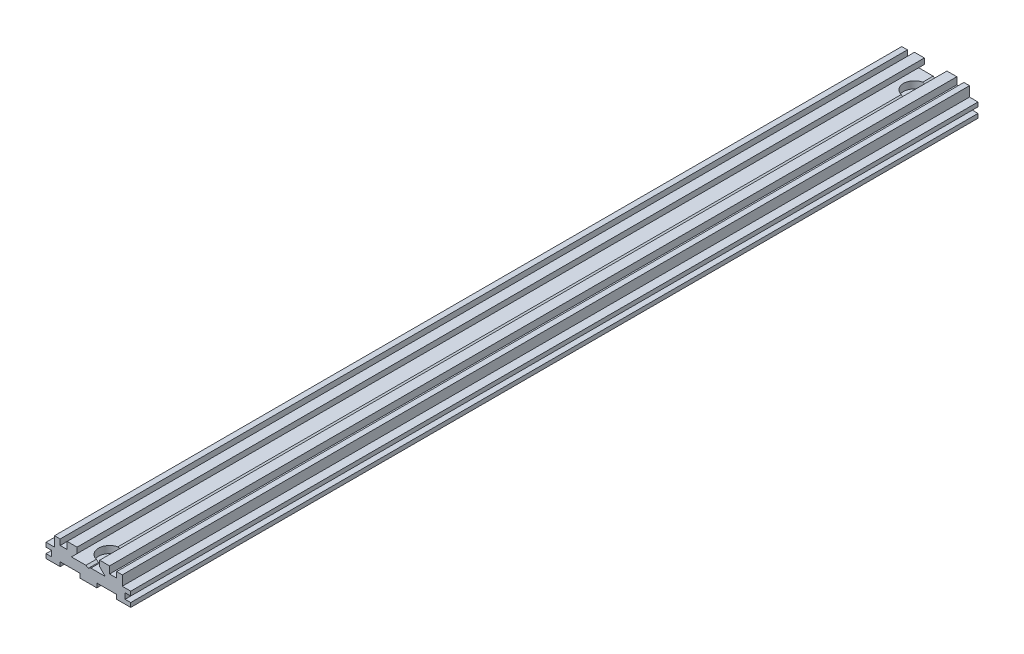
SolidWorks part; units mm, degrees
material "6061 合金"
ref_plane "前视基准面" through (0, 0, 0) normal (0, 0, 1) x (1, 0, 0)
ref_plane "上视基准面" through (0, 0, 0) normal (0, 1, 0) x (1, 0, 0)
ref_plane "右视基准面" through (0, 0, 0) normal (1, 0, 0) x (0, 0, -1)
sketch "草图1" plane through (0, 0, 0) normal (0, 0, 1) x (1, 0, 0)
  line L0 (7.5, 9) -> (7.5, 6.5)
  line L1 (7.5, 6.5) -> (5, 6.5)
  line L2 (5, 6.5) -> (5, 8.5)
  line L3 (30, 0) -> (0, 0)
  line L4 (0, 0) -> (0, 1.5)
  line L5 (15, 0) -> (15, 16.1171) construction
  line L6 (11, 7) -> (9, 5)
  line L7 (19, 7) -> (21, 5)
  line L8 (21, 5) -> (9, 5)
  line L9 (0, 3.5) -> (0, 5)
  line L10 (0, 3.5) -> (2, 3.5)
  line L11 (11, 7) -> (11, 9)
  line L12 (11, 9) -> (7.5, 9)
  line L13 (5, 8.5) -> (3, 8.5)
  line L14 (30, 5) -> (27, 5)
  line L15 (3, 5) -> (0, 5)
  line L16 (19, 7) -> (19, 9)
  line L17 (3, 8.5) -> (3, 5)
  line L18 (22.5, 9) -> (19, 9)
  line L19 (30, 5) -> (0, 5) construction
  line L20 (27, 8.5) -> (27, 5)
  line L21 (30, 0) -> (30, 1.5)
  line L22 (25, 8.5) -> (27, 8.5)
  line L23 (25, 6.5) -> (25, 8.5)
  line L24 (22.5, 6.5) -> (25, 6.5)
  line L25 (22.5, 9) -> (22.5, 6.5)
  line L26 (30, 3.5) -> (30, 5)
  line L27 (0, 1.5) -> (2, 1.5)
  line L28 (2, 3.5) -> (2, 1.5)
  line L29 (30, 3.5) -> (28, 3.5)
  line L31 (30, 1.5) -> (28, 1.5)
  line L32 (28, 3.5) -> (28, 1.5)
  dimension "D2" = 30
  dimension "D3" = 9
  dimension "D4" = 4
  dimension "D5" = 5
  dimension "D6" = 90
  dimension "D7" = 8.5
  dimension "D8" = 24
  dimension "D9" = 12
  dimension "D10" = 6.5
  dimension "D11" = 20
  dimension "D12" = 15
  dimension "D13" = 1.5
  dimension "D14" = 8
  dimension "D15" = 2
  dimension "D16" = 26
extrude "凸台-拉伸1" add sketch "草图1" against normal mid plane 300
sketch "草图3" plane through (0, 0, 150) normal (0, 0, 1) x (1, 0, 0)
  line L0 (0, 0) -> (30, 0) construction
  line L1 (5, 0) -> (12, 0)
  line L2 (5, 0) -> (5, 1.5)
  line L3 (5, 1.5) -> (12, 1.5)
  line L4 (12, 0) -> (12, 1.5)
  line L5 (15, 5) -> (15, 0) construction
  line L6 (18, 0) -> (25, 0)
  line L7 (18, 0) -> (18, 1.5)
  line L8 (18, 1.5) -> (25, 1.5)
  line L9 (25, 0) -> (25, 1.5)
  line L10 (21, 5) -> (9, 5) construction
  line L11 (14.134, 5) -> (15.866, 5)
  line L13 (15.866, 5) -> (15, 4.5)
  line L14 (14.134, 5) -> (15, 4.5)
  dimension "D1" = 120
  dimension "D2" = 0.5
  dimension "D3" = 6
  dimension "D4" = 7
  dimension "D5" = 7
  dimension "D6" = 1.5
  dimension "D7" = 1.5
extrude "切除-拉伸2" cut sketch "草图3" against normal up to next
sketch "草图4" plane through (0, 5, 0) normal (0, 1, 0) x (1, 0, 0)
  line L0 (15, 150) -> (15, -150) construction
  line L1 (21, 150) -> (15.866, 150) construction
  circle A0 centre (15, 142.5) radius 2.25
  dimension "D1" = 4.5
  dimension "D2" = 7.5
extrude "切除-拉伸3" cut sketch "草图4" against normal up to next
sketch "草图5" plane through (0, 5, 0) normal (0, 1, 0) x (1, 0, 0)
  circle A0 centre (15, 142.5) radius 3.9
  dimension "D1" = 7.8
extrude "切除-拉伸4" cut sketch "草图5" against normal blind 2.5
mirror "镜向1" about plane through (0, 0, 0) normal (0, 0, 1) of "切除-拉伸3", "切除-拉伸4"
